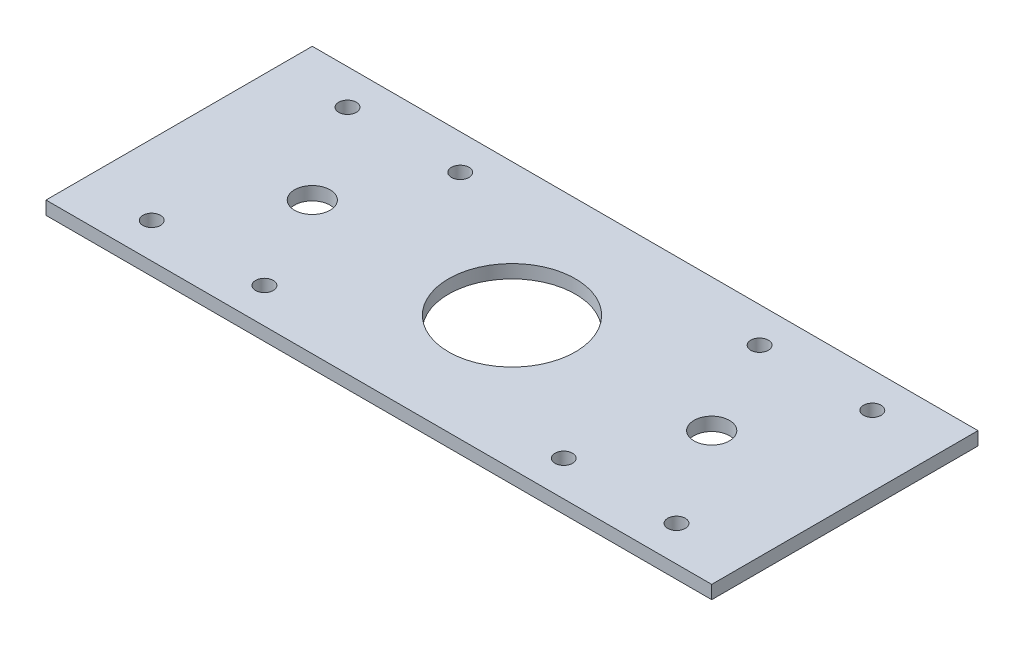
SolidWorks part; units mm, degrees
material "PC High Viscosity"
ref_plane "Front Plane" through (0, 0, 0) normal (0, 0, 1) x (1, 0, 0)
ref_plane "Top Plane" through (0, 0, 0) normal (0, 1, 0) x (1, 0, 0)
ref_plane "Right Plane" through (0, 0, 0) normal (1, 0, 0) x (0, 0, -1)
sketch "Sketch1" plane through (0, 0, 0) normal (0, 1, 0) x (1, 0, 0)
  line L1 (-75, -30) -> (75, -30)
  line L2 (-75, -30) -> (-75, 30)
  line L3 (-75, 30) -> (75, 30)
  line L4 (75, -30) -> (75, 30)
  line L5 (-75, -30) -> (75, 30) construction
  line L6 (-75, 30) -> (75, -30) construction
  point P0 (0, 0)
  dimension "D1" = 150
  dimension "D2" = 60
extrude "Boss-Extrude1" add sketch "Sketch1" along normal blind 3
sketch "Sketch2" plane through (0, 3, 0) normal (0, 1, 0) x (1, 0, 0)
  line L2 (75, 0) -> (-75, 0) construction
  line L6 (75, -30) -> (75, 30) construction
  line L10 (-75, -30) -> (-75, 30) construction
  line L11 (-75, 30) -> (75, 30) construction
  line L12 (0, -30) -> (0, 30) construction
  line L13 (-75, -30) -> (75, -30) construction
  line L14 (-75, 30) -> (75, 30) construction
  circle A0 centre (0, 0) radius 14.2875
  circle A1 centre (59.125, 22.0625) radius 1.9844
  circle A2 centre (33.725, 22.0625) radius 1.9844
  circle A3 centre (33.725, -22.0625) radius 1.9844
  circle A4 centre (59.125, -22.0625) radius 1.9844
  circle A5 centre (-33.725, 22.0625) radius 1.9844
  circle A6 centre (-59.125, 22.0625) radius 1.9844
  circle A7 centre (-59.125, -22.0625) radius 1.9844
  circle A8 centre (-33.725, -22.0625) radius 1.9844
  circle A9 centre (45, 0) radius 4
  circle A10 centre (-45, 0) radius 4
  dimension "D1" = 28.575
  dimension "D2" = 3.9688
  dimension "D3" = 7.9375
  dimension "D4" = 25.4
  dimension "D5" = 15.875
  dimension "D6" = 8
  dimension "D7" = 90
extrude "Cut-Extrude2" cut sketch "Sketch2" against normal through all
equation "\"pulley_pitch_diam\"= 12.73mm"
equation "\"pulley_total_width\"= 16mm"
equation "\"pulley_total_diam\"= 16mm"
equation "\"belt_width\"= 6mm"
equation "\"material_thickness\"= 3mm"
equation "\"shaft_diam\"= 8mm"
equation "\"bearing_od\"= 22mm"
equation "\"bearing_thickness\"= 7mm"
equation "\"D1@Boss-Extrude1\"=\"material_thickness\""
equation "\"D1@Cut-Extrude1\"=\"material_thickness\""
